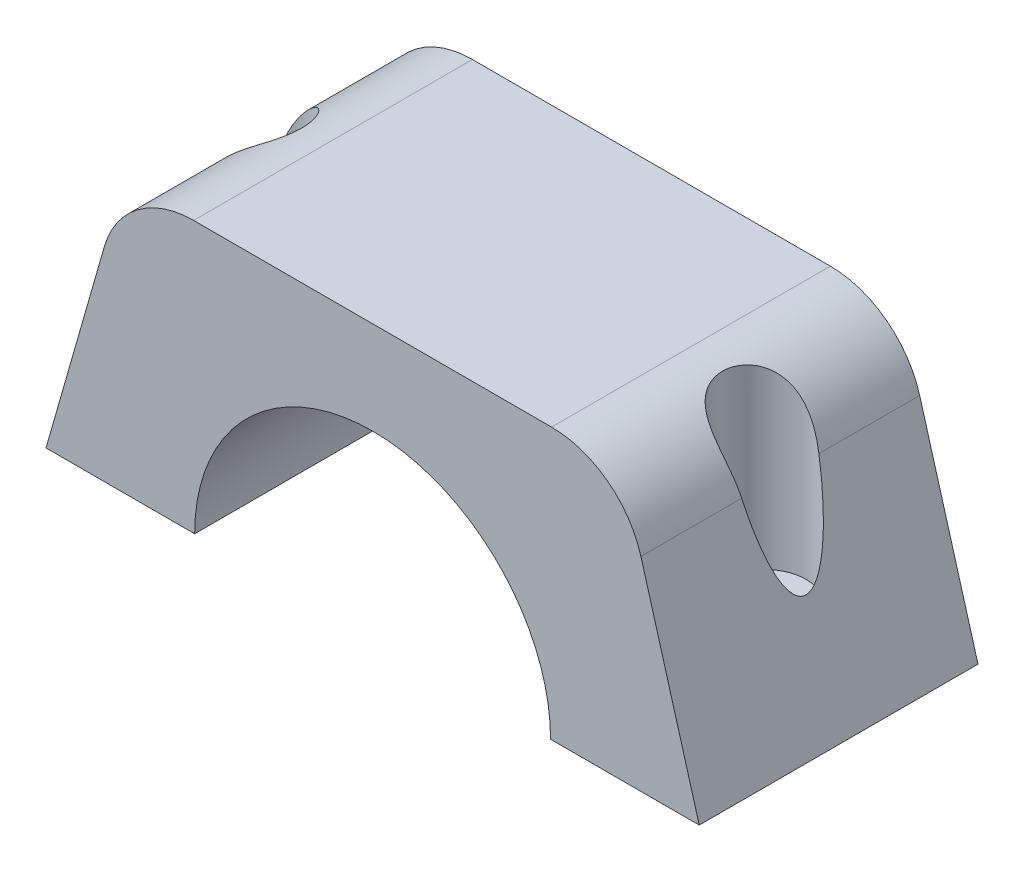
SolidWorks part; units mm, degrees
ref_plane "Front Plane" through (0, 0, 0) normal (0, 0, 1) x (1, 0, 0)
ref_plane "Top Plane" through (0, 0, 0) normal (0, 1, 0) x (1, 0, 0)
ref_plane "Right Plane" through (0, 0, 0) normal (1, 0, 0) x (0, 0, -1)
sketch "Sketch1" plane through (0, 0, 0) normal (0, 0, 1) x (1, 0, 0)
  line L0 (-35.15, 0) -> (35.15, 0) construction
  line L1 (-35.15, 0) -> (-26.7971, 29.15)
  line L2 (-26.7971, 29.15) -> (26.7971, 29.15)
  line L3 (0, 29.15) -> (0, 0) construction
  line L4 (35.15, 0) -> (26.7971, 29.15)
  line L6 (-35.15, 0) -> (-19.15, 0)
  line L7 (19.15, 0) -> (35.15, 0)
  circle A1 centre (0, 0) radius 19.15
  point P11 (0, 19.15)
  dimension "D1" = 10
extrude "Boss-Extrude1" add sketch "Sketch1" along normal blind 30 contours A1 L7 L4 L2 L1 L6
fillet "Fillet1" radius 10 2 edges at (26.7971, 29.15, 15) (-26.7971, 29.15, 15)
sketch "Sketch2" plane through (0, 0, 0) normal (0, -1, 0) x (1, 0, 0)
  line L0 (0, 0) -> (0, 30) construction
  line L1 (19.15, 30) -> (-19.15, 30) construction
  line L2 (-35.15, 30) -> (-19.15, 30) construction
  circle A0 centre (-27.15, 15) radius 2.5
  circle A1 centre (27.15, 15) radius 2.5
  point P7 (0, 0)
  point P8 (0, 15)
  point P11 (0, 0)
  point P12 (-27.15, 30)
  dimension "D1" = 5
extrude "Cut-Extrude1" cut sketch "Sketch2" against normal through all
sketch "Sketch3" plane through (0, 29.15, 0) normal (0, 1, 0) x (1, 0, 0)
  line L0 (0, 0) -> (0, -30) construction
  line L1 (-19.2601, -30) -> (19.2601, -30) construction
  arc A0 (28.8732, -13.1888) -> (28.8732, -16.8112) centre (27.15, -15) ccw construction
  arc A1 (28.8732, -13.1888) -> (28.8732, -16.8112) centre (27.15, -15) ccw
  circle A2 centre (27.15, -15) radius 4.5
  circle A3 centre (-27.15, -15) radius 4.5
  dimension "D1" = 9
extrude "Cut-Extrude2" cut sketch "Sketch3" against normal blind 20
